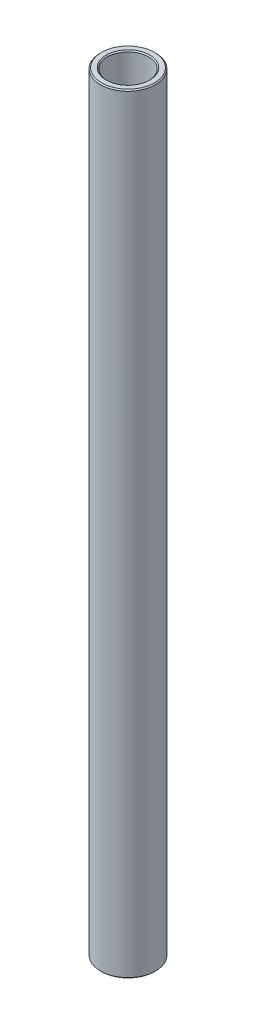
SolidWorks part; units mm, degrees
ref_plane "Front Plane" through (0, 0, 0) normal (0, 0, 1) x (1, 0, 0)
ref_plane "Top Plane" through (0, 0, 0) normal (0, 1, 0) x (1, 0, 0)
ref_plane "Right Plane" through (0, 0, 0) normal (1, 0, 0) x (0, 0, -1)
sketch "Sketch1" plane through (0, 0, 0) normal (0, 0, 1) x (1, 0, 0)
  line L0 (4.7625, 9.525) -> (4.7625, 186.9852)
  line L1 (4.7625, 186.9852) -> (6.35, 186.9852)
  line L2 (6.35, 186.9852) -> (6.35, 9.525)
  line L3 (6.35, 9.525) -> (4.7625, 9.525)
  line L6 (0, 0) -> (0, 196.5102) construction
  dimension "D1" = 9.525
  dimension "D2" = 9.525
  dimension "D3" = 12.7
  dimension "D4" = 9.525
revolve "Revolve1" add sketch "Sketch1" angle 360 about L6
chamfer "Chamfer1" distance 0.254 angle 45 4 edges at (6.35, 186.9852, 0) (4.7625, 186.9852, 0) (4.7625, 9.525, 0) (6.35, 9.525, 0)
equation "\"D4@Sketch1\"=\"D1@Sketch1\""
